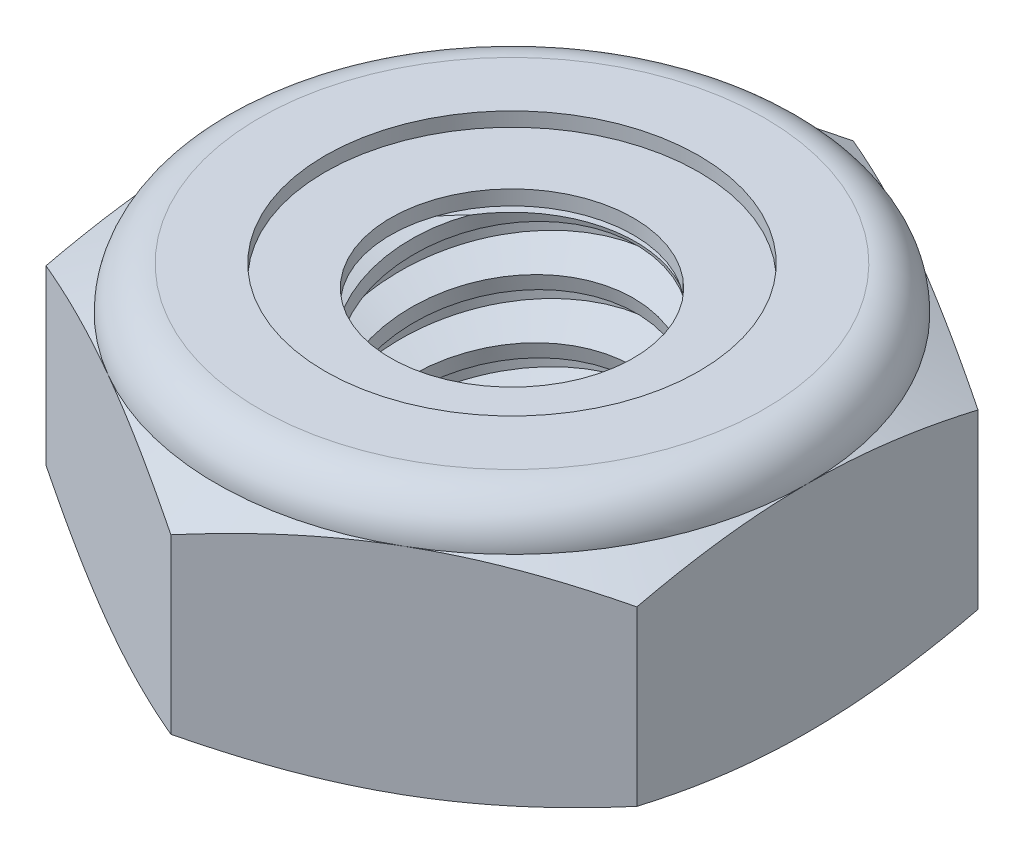
SolidWorks part; units mm, degrees
ref_plane "Front" through (0, 0, 0) normal (0, 0, 1) x (1, 0, 0)
ref_plane "Top" through (0, 0, 0) normal (0, 1, 0) x (1, 0, 0)
ref_plane "Right" through (0, 0, 0) normal (1, 0, 0) x (0, 0, -1)
sketch "Sketch1" plane through (0, 0, 0) normal (0, 1, 0) x (1, 0, 0)
  line L1 (0, 3.6662) -> (-3.175, 1.8331)
  line L2 (-3.175, 1.8331) -> (-3.175, -1.8331)
  line L3 (-3.175, -1.8331) -> (0, -3.6662)
  line L4 (0, -3.6662) -> (3.175, -1.8331)
  line L5 (3.175, -1.8331) -> (3.175, 1.8331)
  line L6 (3.175, 1.8331) -> (0, 3.6662)
  circle A0 centre (0, 0) radius 3.175 construction
  dimension "Hex Flats" = 6.35
extrude "Extrude1" add sketch "Sketch1" along normal blind 2.7781
sketch "Sketch2" plane through (0, 0, 0) normal (1, 0, 0) x (0, 0, -1)
  line L0 (-1.5875, 0) -> (-1.5875, 2.7781) construction
  line L1 (0, 0) -> (1.5875, 0)
  line L2 (0, 0) -> (0, 2.7781)
  line L3 (0, 2.7781) -> (1.5875, 2.7781)
  line L4 (1.5875, 0) -> (1.5875, 2.7781)
  line L5 (-1.8331, 2.7781) -> (1.8331, 2.7781) construction
  line L7 (0, -1.5875) -> (0, 0) construction
  dimension "Thread Dia" = 3.175
revolve "Revolve1" add sketch "Sketch2" angle 360 about L7
sketch "Sketch3" plane through (0, 0, 0) normal (1, 0, 0) x (0, 0, -1)
  line L0 (1.5875, 2.7781) -> (-1.5875, 2.7781) construction
  line L1 (-1.5875, 2.7781) -> (-1.5875, 2.1431) construction
  line L2 (-1.5875, 2.1431) -> (1.5875, 2.7781) construction
  line L3 (1.5875, 2.7781) -> (1.6031, 2.7003) construction
  line L4 (1.6031, 2.7003) -> (1.712, 2.1555)
  line L5 (1.712, 2.1555) -> (1.3361, 2.2826)
  line L6 (1.3361, 2.2826) -> (1.305, 2.4383)
  line L7 (1.305, 2.4383) -> (1.6031, 2.7003)
  line L8 (1.3205, 2.3605) -> (1.6576, 2.4279) construction
  line L9 (1.5875, 2.7781) -> (1.5875, 2.4139) construction
  line L10 (1.5875, 2.4139) -> (-1.5875, 1.7789) construction
  line L11 (-1.5875, 1.7789) -> (-1.5875, 2.1431) construction
  line L12 (-0.1364, 2.7781) -> (0.1364, 1.4146) construction
  line L13 (-1.5875, 0) -> (-1.5875, 2.7781) construction
  line L14 (0, 2.7781) -> (1.5875, 2.7781) construction
  line L15 (1.5875, 0) -> (1.5875, 2.7781) construction
  point P13 (0, 2.0964)
  dimension "D1" = 0.0794
  dimension "D2" = 0.1588
  dimension "Thread Pitch" = 0.635
  dimension "D4" = 60
  dimension "D5" = 0.635
revolve "Cut-Revolve1" cut sketch "Sketch3" angle 360 about L12
pattern_linear "LPattern1" count 4 spacing 0.635 along (0, -1, 0) count 2 spacing 0.635 along (0, 1, 0) of "Cut-Revolve1"
sketch "Sketch4" plane through (0, 0, 0) normal (1, 0, 0) x (0, 0, -1)
  line L0 (0, 2.7781) -> (1.5875, 2.7781)
  line L1 (1.5875, 2.7781) -> (1.305, 2.6464)
  line L2 (1.305, 2.6464) -> (1.305, 0.1318)
  line L3 (1.305, 0.1318) -> (1.5875, 0)
  line L4 (1.5875, 0) -> (0, 0)
  line L5 (0, 0) -> (0, 2.7781)
  line L6 (1.5875, 0) -> (1.5875, 2.7781) construction
  line L7 (0, 2.7781) -> (1.5875, 2.7781) construction
  line L8 (0, 0) -> (1.5875, 0) construction
  line L9 (0, 0) -> (0, 2.7781) construction
  line L10 (0, 2.7781) -> (0, 3.0899) construction
  dimension "D1" = 25
revolve "Cut-Revolve2" cut sketch "Sketch4" angle 360 about L10
combine bodies "Combine1" operation type subtract main body 112 bodies to subtract 111
sketch "Sketch5" plane through (0, 0, 0) normal (1, 0, 0) x (0, 0, -1)
  line L0 (0, 0) -> (3.175, 0)
  line L1 (3.175, 0) -> (3.6662, 0.229)
  line L2 (3.6662, 0.229) -> (3.6662, 2.0861)
  line L3 (3.6662, 2.0861) -> (3.175, 2.3151)
  line L4 (2.712, 2.7781) -> (2.712, 4.0481)
  line L5 (2.712, 4.0481) -> (4.9362, 4.0481)
  line L6 (4.9362, 4.0481) -> (4.9362, -1.27)
  line L7 (4.9362, -1.27) -> (0, -1.27)
  line L8 (0, -1.27) -> (0, 0)
  line L9 (3.175, 2.3151) -> (3.175, 0) construction
  line L10 (0, 0) -> (1.5875, 0) construction
  line L13 (3.6662, 1.1576) -> (4.9362, 1.1576) construction
  line L14 (3.6662, 2.7781) -> (3.6662, 0) construction
  line L15 (0, 0) -> (0, 4.0481) construction
  line L20 (0, 4.0481) -> (2.712, 4.0481) construction
  line L22 (0, 2.7781) -> (1.5875, 2.7781) construction
  arc A0 (3.175, 2.3151) -> (2.712, 2.7781) centre (2.712, 2.3151) ccw
  dimension "D1" = 25
  dimension "D2" = 1.27
  dimension "D3" = 2.7781
  dimension "D4" = 0.463
revolve "Cut-Revolve3" cut sketch "Sketch5" angle 360 about L15
sketch "Sketch6" plane through (0, 0, 0) normal (1, 0, 0) x (0, 0, -1)
  line L0 (0, 2.3151) -> (3.0226, 2.3151)
  line L1 (2.712, 2.6257) -> (2.0085, 2.6257)
  line L2 (0, 4.0481) -> (0, 2.3151)
  line L3 (2.0085, 4.0481) -> (0, 4.0481)
  line L4 (0, 4.0481) -> (2.712, 4.0481) construction
  line L5 (0, 0) -> (0, 4.0481) construction
  line L6 (0, 4.0481) -> (0, 44.323) construction
  line L7 (2.0085, 2.6257) -> (2.0085, 4.0481)
  line L8 (2.712, 2.7781) -> (2.712, 2.6257) construction
  line L9 (2.0085, 2.6257) -> (1.305, 2.6257) construction
  line L10 (1.305, 2.6257) -> (1.305, 2.6464) construction
  arc A0 (3.0226, 2.3151) -> (2.712, 2.6257) centre (2.712, 2.3151) ccw
  arc A1 (3.175, 2.3151) -> (2.712, 2.7781) centre (2.712, 2.3151) ccw construction
  dimension "D1" = 0.1524
revolve "Cut-Revolve4" cut sketch "Sketch6" angle 360 about L6
sketch "Sketch7" plane through (0, 0, 0) normal (1, 0, 0) x (0, 0, -1)
  line L0 (1.305, 2.3913) -> (2.9337, 2.3913)
  line L1 (2.712, 2.5495) -> (1.305, 2.5495)
  line L2 (1.305, 2.5495) -> (1.305, 2.3913)
  line L3 (1.305, 2.3913) -> (0, 2.3913) construction
  line L4 (0, 2.3913) -> (0, 2.5495) construction
  line L5 (0, 2.5495) -> (1.305, 2.5495) construction
  line L6 (1.305, 2.3913) -> (1.305, 2.3151) construction
  line L7 (0, 2.3151) -> (3.0226, 2.3151) construction
  line L8 (2.712, 2.5495) -> (2.712, 2.6257) construction
  arc A0 (2.9337, 2.3913) -> (2.712, 2.5495) centre (2.712, 2.3151) ccw
  arc A2 (3.0226, 2.3151) -> (2.712, 2.6257) centre (2.712, 2.3151) ccw construction
  dimension "D1" = 0.0762
revolve "Revolve2" add sketch "Sketch7" angle 360 about L4
equation "\"D1@Sketch3\"=\"Thread Pitch@Sketch3\"/8"
equation "\"D2@Sketch3\"=\"Thread Pitch@Sketch3\"/4"
equation "\"D5@Sketch3\"=\"Thread Pitch@Sketch3\""
equation "\"D4@LPattern1\"=\"Thread Pitch@Sketch3\""
equation "\"D3@LPattern1\"=\"Thread Pitch@Sketch3\""
equation "\"D1@LPattern1\"=\"Height@Extrude1\"/\"Thread Pitch@Sketch3\""
equation "\"D4@Sketch5\"=\"Height@Extrude1\"/6"
